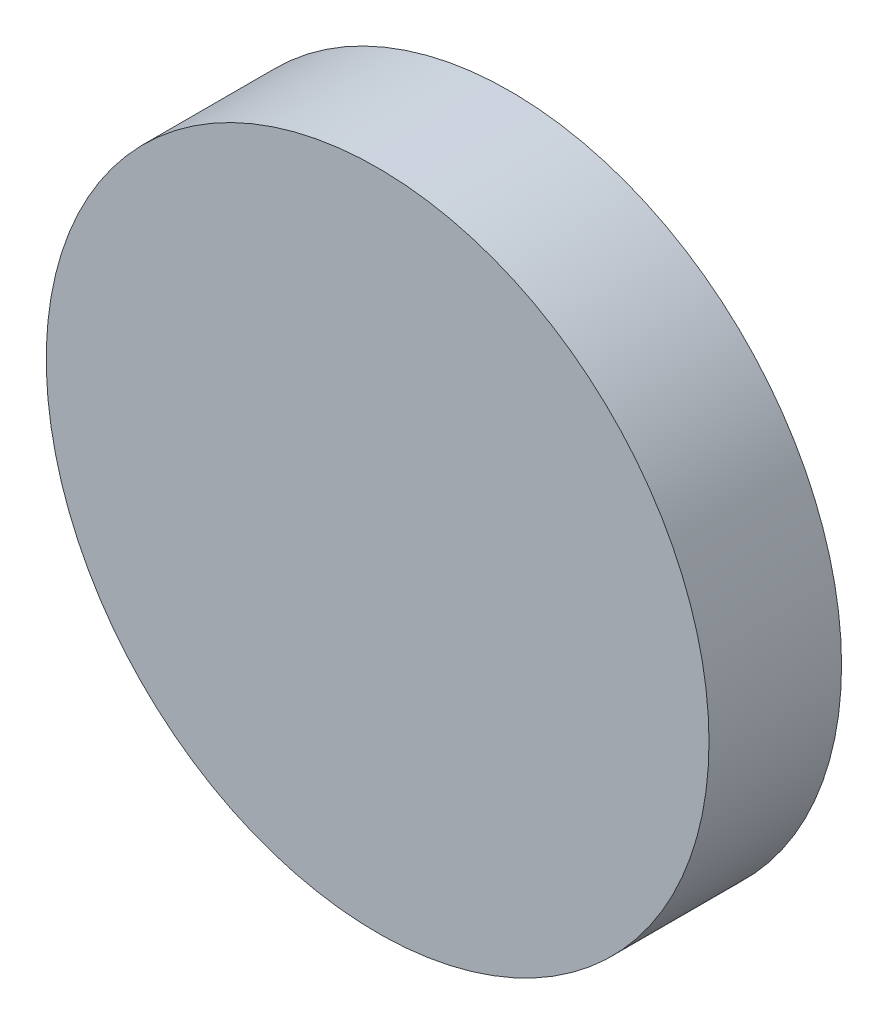
SolidWorks part; units mm, degrees
ref_plane "Front Plane" through (0, 0, 0) normal (0, 0, 1) x (1, 0, 0)
ref_plane "Top Plane" through (0, 0, 0) normal (0, 1, 0) x (1, 0, 0)
ref_plane "Right Plane" through (0, 0, 0) normal (1, 0, 0) x (0, 0, -1)
sketch "Sketch1" plane through (0, 0, 0) normal (0, 0, 1) x (1, 0, 0)
  circle A0 centre (0, 0) radius 30
extrude "Boss-Extrude1" add sketch "Sketch1" along normal blind 12
